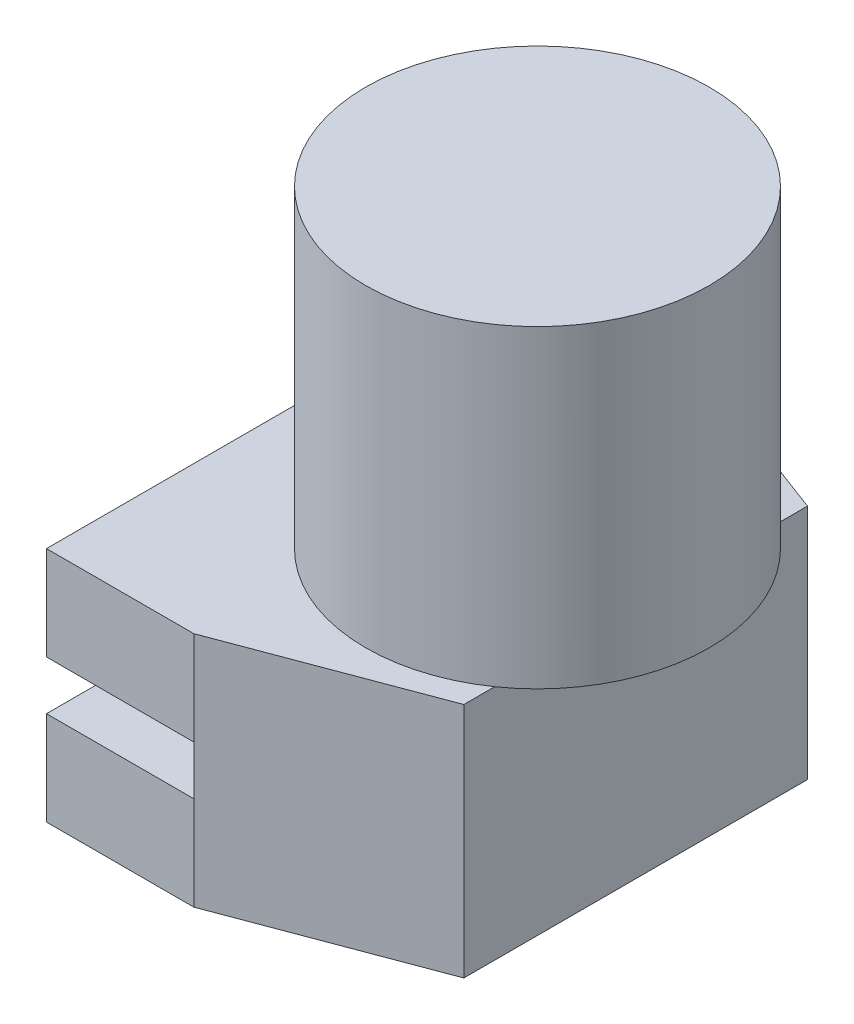
SolidWorks part; units mm, degrees
material "6061 Alloy"
ref_plane "Front Plane" through (0, 0, 0) normal (0, 0, 1) x (1, 0, 0)
ref_plane "Top Plane" through (0, 0, 0) normal (0, 1, 0) x (1, 0, 0)
ref_plane "Right Plane" through (0, 0, 0) normal (1, 0, 0) x (0, 0, -1)
sketch "Base" plane through (0, 0, 0) normal (0, 1, 0) x (1, 0, 0)
  line L0 (0, -63.5) -> (0, 63.5)
  line L1 (0, 63.5) -> (38.1, 63.5)
  line L2 (38.1, 63.5) -> (88.9, 44.45)
  line L3 (88.9, 44.45) -> (88.9, -44.45)
  line L4 (88.9, -44.45) -> (38.1, -63.5)
  line L5 (38.1, -63.5) -> (0, -63.5)
  line L6 (38.1, 63.5) -> (38.1, -63.5) construction
  point P6 (50.0205, -66.0985)
  point P7 (129.9233, -26.7967)
  point P9 (130.1978, 33.8757)
  point P10 (88.9, 0)
  point P11 (47.0387, 63.5)
  point P12 (121.0595, 44.45)
  point P13 (0, 0)
  point P14 (0, 0)
  dimension "D1" = 127
  dimension "D2" = 88.9
  dimension "D3" = 38.1
  dimension "D4" = 88.9
extrude "Base Approximate" add sketch "Base" along normal mid plane 61.2648
sketch "Beam Channel Cross Section" plane through (0, 0, 0) normal (0, 0, 1) x (1, 0, 0)
  line L1 (0, -6.35) -> (38.1, -6.35)
  line L2 (0, -6.35) -> (0, 6.35)
  line L3 (0, 6.35) -> (38.1, 6.35)
  line L4 (38.1, -6.35) -> (38.1, 6.35)
  dimension "D1" = 12.7
  dimension "D2" = 38.1
extrude "Beam Channel" cut sketch "Beam Channel Cross Section" against normal through all both and the other way through all
sketch "Hole Cross Section" plane through (0, 30.6324, 0) normal (0, 1, 0) x (1, 0, 0)
  line L3 (0, 63.5) -> (0, -63.5) construction
  line L4 (88.9, 0) -> (38.1, 0) construction
  line L5 (88.9, -44.45) -> (88.9, 44.45) construction
  line L6 (38.1, 63.5) -> (38.1, -63.5) construction
  circle A1 centre (63.5, 0) radius 19.05
  point P0 (63.5, 0)
  point P5 (0, 0)
  point P10 (0, 0)
  point P15 (0, 0)
  dimension "D1" = 38.1
extrude "Hole" cut sketch "Hole Cross Section" against normal blind 25.4
sketch "Round Part Cross Section" plane through (0, 30.6324, 0) normal (0, 1, 0) x (1, 0, 0)
  circle A0 centre (63.5, 0) radius 44.45
  circle A1 centre (63.5, 0) radius 19.05 construction
  dimension "D1" = 88.9
extrude "Round Part" add sketch "Round Part Cross Section" along normal blind 81.153
